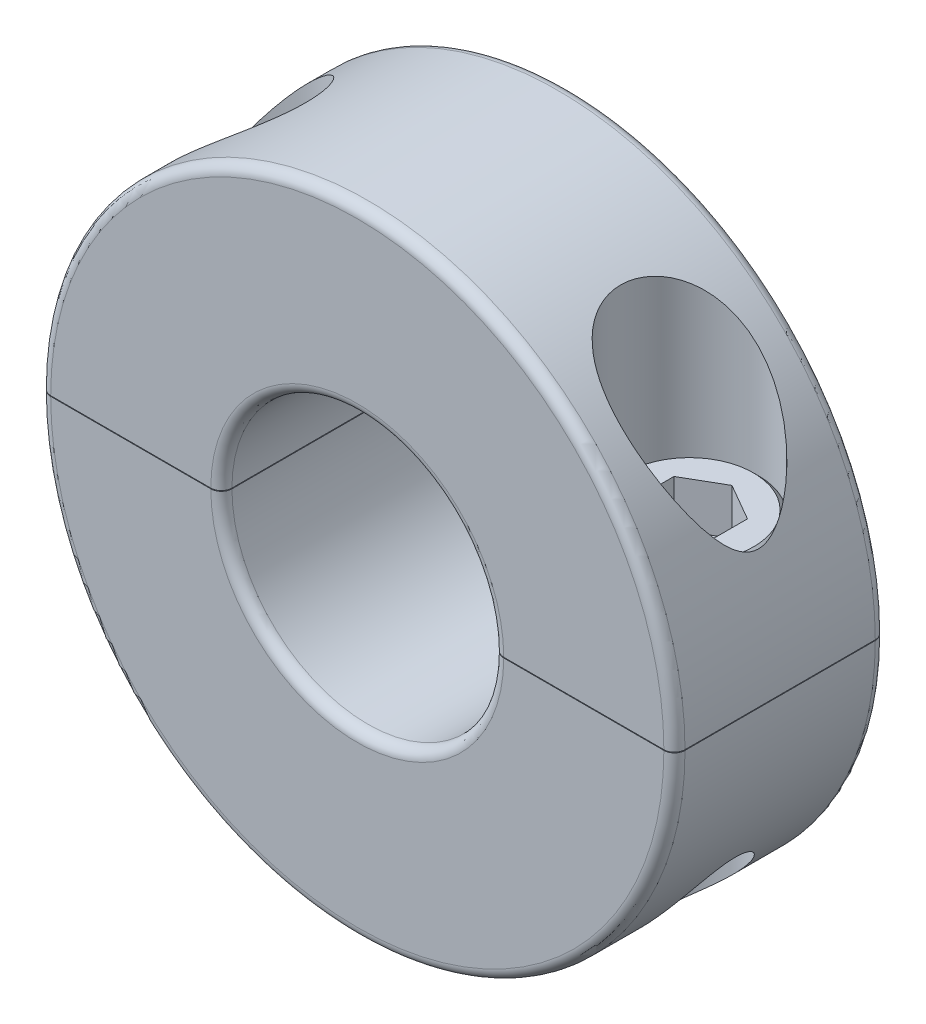
SolidWorks part; units mm, degrees
material "Alloy Steel"
ref_plane "Front Plane" through (0, 0, 0) normal (0, 0, 1) x (1, 0, 0)
ref_plane "Top Plane" through (0, 0, 0) normal (0, 1, 0) x (1, 0, 0)
ref_plane "Right Plane" through (0, 0, 0) normal (1, 0, 0) x (0, 0, -1)
sketch "Sketch1" plane through (0, 0, 0) normal (0, 0, 1) x (1, 0, 0)
  line L0 (-16.6687, 0) -> (-7.1438, 0) construction
  line L1 (-16.6687, 0.0167) -> (-7.1438, 0.0167)
  line L2 (-16.6687, -0.0167) -> (-7.1438, -0.0167)
  line L3 (7.1438, 0.0167) -> (16.6687, 0.0167)
  line L4 (7.1438, -0.0167) -> (16.6687, -0.0167)
  line L5 (0, 0) -> (0, 16.6687) construction
  circle A0 centre (0, 0) radius 16.6687 construction
  circle A1 centre (0, 0) radius 7.1438 construction
  arc A2 (-16.6687, 0.0167) -> (16.6687, 0.0167) centre (0, 0.0167) cw
  arc A3 (-16.6687, -0.0167) -> (16.6687, -0.0167) centre (0, -0.0167) ccw
  arc A4 (-7.1438, 0.0167) -> (7.1438, 0.0167) centre (0, 0.0167) cw
  arc A5 (-7.1438, -0.0167) -> (7.1438, -0.0167) centre (0, -0.0167) ccw
  point P4 (16.6687, 0)
  dimension "Bore Dia" = 14.2875
  dimension "OD" = 33.3375
  dimension "Separation" = 0.0333
extrude "Extrude1" add sketch "Sketch1" along normal mid plane 11.1125
sketch "Sketch4" plane through (0, 0, 0) normal (0, 0, 1) x (1, 0, 0)
  line L0 (-11.9062, 16.6854) -> (-8.2868, 16.6854)
  line L1 (-8.2868, 16.6854) -> (-8.2868, 1.2232)
  line L2 (-8.2868, 1.2232) -> (-9.4933, 1.2232)
  line L3 (-9.4933, 1.2232) -> (-9.4933, -16.6854)
  line L4 (-9.4933, -16.6854) -> (-11.9062, -16.6854)
  line L5 (-11.9062, -16.6854) -> (-11.9062, 16.6854)
  line L6 (-8.2868, 6.0492) -> (-15.5257, 6.0492) construction
  line L7 (-11.9062, 16.6854) -> (-11.9062, 19.2254) construction
  line L8 (-8.2868, 16.6854) -> (0, 16.6854) construction
  line L9 (0, -16.6854) -> (-9.4933, -16.6854) construction
  line L10 (-16.6687, 0) -> (-7.1438, 0) construction
  line L11 (-16.6687, 0.0167) -> (-7.1438, 0.0167) construction
  circle A0 centre (0, 0) radius 16.6687 construction
  arc A1 (16.6687, 0.0167) -> (-16.6687, 0.0167) centre (0, 0.0167) ccw construction
  circle A2 centre (0, 0) radius 7.1438 construction
  arc A3 (-16.6687, -0.0167) -> (16.6687, -0.0167) centre (0, -0.0167) ccw construction
  point P13 (-11.9062, 0)
  point P19 (-11.9062, 0)
  point P20 (-11.9062, 6.0492)
  dimension "D1" = 4.826
  dimension "D2" = 9.525
  dimension "D3" = 1.2065
  dimension "D4" = 7.239
  dimension "D5" = 2.54
  dimension "Screw Dia" = 4.826
revolve "Cut-Revolve1" cut sketch "Sketch4" angle 360 about L5
sketch "Sketch6" plane through (0, 0, 0) normal (0, 0, 1) x (1, 0, 0)
  line L0 (-11.9062, 6.0492) -> (-8.2868, 6.0492)
  line L1 (-8.2868, 6.0492) -> (-15.5257, 6.0492) construction
  line L2 (-8.2868, 6.0492) -> (-8.2868, 1.2232)
  line L3 (-8.2868, 1.2232) -> (-9.4933, 1.2232)
  line L4 (-9.4933, 1.2232) -> (-9.4933, -8.4288)
  line L5 (-9.4933, 1.2232) -> (-9.4933, -16.6854) construction
  line L6 (-9.4933, -8.4288) -> (-11.9062, -8.4288)
  line L7 (-11.9062, -16.6854) -> (-11.9062, 16.6854) construction
  line L8 (-11.9062, -8.4288) -> (-11.9062, 6.0492)
  line L9 (-9.4933, -8.4288) -> (-14.3192, -8.4288) construction
  dimension "Head Ht" = 4.826
  dimension "Screw Lg" = 14.478
revolve "Revolve1" add sketch "Sketch6" angle 360 about L8
mirror "Mirror1" about plane through (0, 0, 0) normal (1, 0, 0) of "Cut-Revolve1"
sketch "Sketch7" plane through (0, 6.0492, 0) normal (0, 1, 0) x (-1, 0, 0)
  line L1 (11.9063, -2.229) -> (13.8366, -1.1145)
  line L2 (13.8366, -1.1145) -> (13.8366, 1.1145)
  line L3 (13.8366, 1.1145) -> (11.9062, 2.229)
  line L4 (11.9062, 2.229) -> (9.9759, 1.1145)
  line L5 (9.9759, 1.1145) -> (9.9759, -1.1145)
  line L6 (9.9759, -1.1145) -> (11.9063, -2.229)
  circle A0 centre (11.9062, 0) radius 1.9304 construction
  dimension "D1" = 3.8608
extrude "Cut-Extrude2" cut sketch "Sketch7" against normal blind 2.413
mirror "Mirror2" about plane through (0, 0, 0) normal (1, 0, 0) of bodies 149 147
fillet "Fillet1" radius 0.5556 4 edges at (0, 7.1604, -5.5562) (0, 7.1604, 5.5562) (0, 16.6854, -5.5562) (0, 16.6854, 5.5562)
fillet "Fillet2" radius 0.5556 4 edges at (0, -16.6854, -5.5562) (0, -16.6854, 5.5562) (0, -7.1604, -5.5562) (0, -7.1604, 5.5562)
chamfer "Chamfer1" distance 0.254 angle 45 1 edges at (11.9062, 6.0492, -3.6195)
chamfer "Chamfer2" distance 0.254 angle 45 1 edges at (-11.9062, 6.0492, -3.6195)
equation "\"D1@Sketch4\" = \"Screw Dia@Sketch4\""
equation "\"D4@Sketch4\" = \"Screw Dia@Sketch4\"*1.5"
equation "\"D1@Sketch7\" = \"Screw Dia@Sketch4\"*.8"
equation "\"D1@Cut-Extrude2\" = \"Head Ht@Sketch6\"/2"
equation "\"D3@Sketch4\" = \"D1@Sketch4\"*.25"
equation "\"D1@Fillet1\" = \"Width@Extrude1\"*.05"
equation "\"D1@Fillet2\" = \"D1@Fillet1\""
equation "\"Screw Lg@Sketch6\" = \"Head Ht@Sketch6\"*3"
